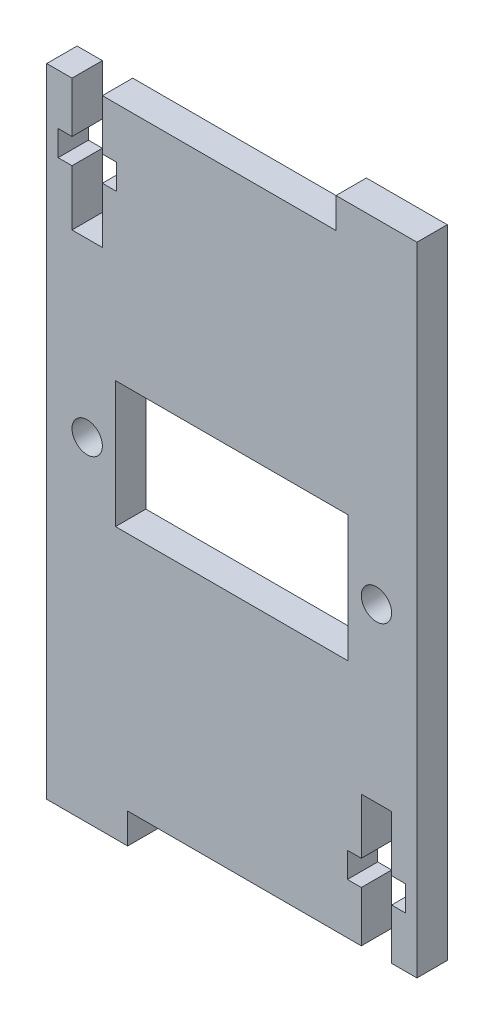
SolidWorks part; units mm, degrees
ref_plane "Plano frontal" through (0, 0, 0) normal (0, 0, 1) x (1, 0, 0)
ref_plane "Plano superior" through (0, 0, 0) normal (0, 1, 0) x (1, 0, 0)
ref_plane "Plano direito" through (0, 0, 0) normal (1, 0, 0) x (0, 0, -1)
sketch "Esboço1" plane through (0, 0, 0) normal (0, 0, 1) x (1, 0, 0)
  line L16 (11.2425, -13) -> (11.2425, -8)
  line L17 (11.2425, 0) -> (8.2425, 0)
  line L18 (8.2425, 0) -> (8.2425, -5.5)
  line L19 (12.6175, -5.5) -> (11.2425, -5.5)
  line L20 (6.8675, -5.5) -> (6.8675, -8)
  line L21 (6.8675, -8) -> (8.2425, -8)
  line L22 (12.6175, -8) -> (12.6175, -5.5)
  line L23 (11.2425, -8) -> (12.6175, -8)
  line L24 (11.2425, -5.5) -> (11.2425, 0)
  line L25 (8.2425, -5.5) -> (6.8675, -5.5)
  line L26 (8.2425, -8) -> (8.2425, -13)
  line L35 (-22.8575, 47) -> (-22.8575, 25.3)
  line L58 (13.7425, 50) -> (13.7425, -13)
  line L59 (13.7425, -13) -> (11.2425, -13)
  line L61 (-14.8575, -16) -> (-22.8575, -16)
  line L62 (-22.8575, -16) -> (-22.8575, -13)
  line L63 (-14.8575, -16) -> (-14.8575, -13)
  line L65 (6.9425, 23.25) -> (-16.0575, 23.25)
  line L67 (5.7425, 47) -> (5.7425, 50)
  line L69 (13.7425, 50) -> (5.7425, 50)
  line L70 (-16.0575, 23.25) -> (-16.0575, 10.75)
  line L71 (5.7425, 47) -> (-17.3575, 47)
  line L76 (-15.9825, 39.5) -> (-15.9825, 42)
  line L77 (-20.3575, 47) -> (-20.3575, 42)
  line L78 (-20.3575, 34) -> (-17.3575, 34)
  line L79 (-17.3575, 34) -> (-17.3575, 39.5)
  line L80 (-21.7325, 39.5) -> (-20.3575, 39.5)
  line L81 (-15.9825, 42) -> (-17.3575, 42)
  line L82 (-21.7325, 42) -> (-21.7325, 39.5)
  line L83 (-20.3575, 42) -> (-21.7325, 42)
  line L84 (-20.3575, 39.5) -> (-20.3575, 34)
  line L85 (-17.3575, 39.5) -> (-15.9825, 39.5)
  line L86 (-17.3575, 42) -> (-17.3575, 47)
  line L88 (-20.3575, 47) -> (-22.8575, 47)
  line L89 (8.2425, -13) -> (-14.8575, -13)
  line L90 (-22.8575, -13) -> (-22.8575, 25.3)
  line L91 (-16.0575, 10.75) -> (6.9425, 10.75)
  line L92 (6.9425, 10.75) -> (6.9425, 23.25)
  circle A0 centre (-18.8575, 17) radius 1.5
  circle A1 centre (9.7425, 17) radius 1.5
extrude "Ressalto-extrusão1" add sketch "Esboço1" along normal blind 3
